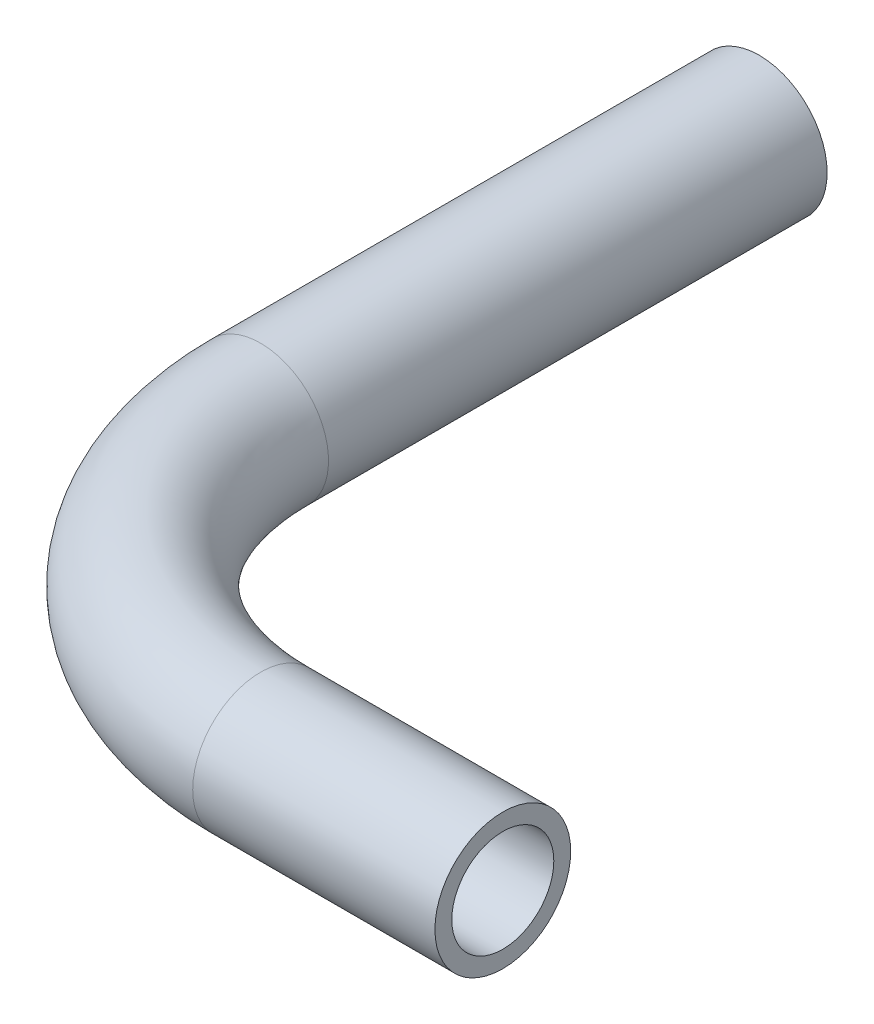
SolidWorks part; units mm, degrees
material "ПК/АБС"
ref_plane "Спереди" through (0, 0, 0) normal (0, 0, 1) x (1, 0, 0)
ref_plane "Сверху" through (0, 0, 0) normal (0, 1, 0) x (1, 0, 0)
ref_plane "Справа" through (0, 0, 0) normal (1, 0, 0) x (0, 0, -1)
sketch "Эскиз1" plane through (0, 0, 0) normal (0, 0, 1) x (1, 0, 0)
  circle A0 centre (0, 0) radius 3.58
  circle A1 centre (0, 0) radius 4.765
  dimension "D1" = 7.16
  dimension "D2" = 9.53
sketch3d "Трехмерный эскиз1"
  line L0 (0, 0, 0) -> (0, 0, 35)
  line L1 (20, 0, 55) -> (37, 0, 55)
  arc A0 (0, 0, 35) -> (20, 0, 55) centre (20, 0, 35) ccw
  point P3 (20, 20, 35)
  dimension "D1" = 20
  dimension "D2" = 37
  dimension "D3" = 55
sweep "По траектории1" add profiles "Эскиз1" path "Трехмерный эскиз1"
ref_plane "Плоскость1" through (0, 0, 45) normal (0, 0, 1) x (1, 0, 0)
